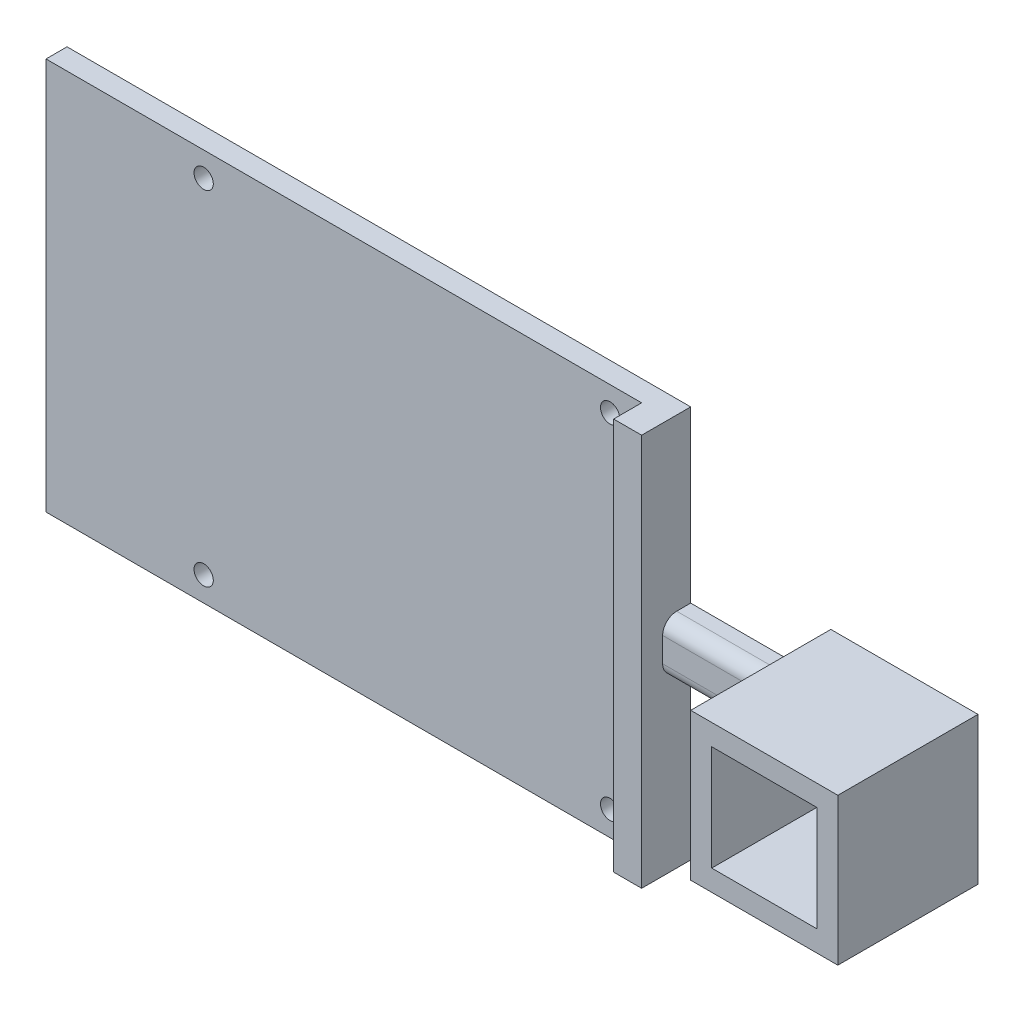
SolidWorks part; units mm, degrees
ref_plane "Front Plane" through (0, 0, 0) normal (0, 0, 1) x (1, 0, 0)
ref_plane "Top Plane" through (0, 0, 0) normal (0, 1, 0) x (1, 0, 0)
ref_plane "Right Plane" through (0, 0, 0) normal (1, 0, 0) x (0, 0, -1)
sketch "Sketch2" plane through (0, 0, 0) normal (0, 0, 1) x (1, 0, 0)
  line L1 (10.5, -10.5) -> (-10.5, -10.5)
  line L2 (10.5, -10.5) -> (10.5, 10.5)
  line L3 (10.5, 10.5) -> (-10.5, 10.5)
  line L4 (-10.5, -10.5) -> (-10.5, 10.5)
  line L5 (10.5, -10.5) -> (-10.5, 10.5) construction
  line L6 (10.5, 10.5) -> (-10.5, -10.5) construction
  point P0 (0, 0)
  dimension "D1" = 21
extrude "Boss-Extrude1" add sketch "Sketch2" along normal blind 20
sketch "Sketch3" plane through (0, 0, 20) normal (0, 0, 1) x (1, 0, 0)
  line L1 (7.5, -7.5) -> (-7.5, -7.5)
  line L2 (7.5, -7.5) -> (7.5, 7.5)
  line L3 (7.5, 7.5) -> (-7.5, 7.5)
  line L4 (-7.5, -7.5) -> (-7.5, 7.5)
  line L5 (7.5, -7.5) -> (-7.5, 7.5) construction
  line L6 (7.5, 7.5) -> (-7.5, -7.5) construction
  point P0 (0, 0)
  dimension "D1" = 15
  dimension "D2" = 15
extrude "Cut-Extrude1" cut sketch "Sketch3" against normal blind 20
sketch "Sketch4" plane through (-10.5, 0, 0) normal (-1, 0, 0) x (0, 0, 1)
  line L1 (0, 3.75) -> (4, 3.75)
  line L2 (0, 3.75) -> (0, -3.75)
  line L3 (0, -3.75) -> (4, -3.75)
  line L4 (4, 3.75) -> (4, -3.75)
  point P4 (0, 0)
  dimension "D1" = 7.5
  dimension "D2" = 4
  dimension "D3" = 10.5
extrude "Boss-Extrude2" add sketch "Sketch4" along normal blind 20
fillet "Fillet2" radius 2 2 edges at (-20.5, -3.75, 4) (-20.5, 3.75, 4)
sketch "Sketch5" plane through (-30.5, 0, 0) normal (-1, 0, 0) x (0, 0, 1)
  line L0 (0, 0) -> (4, 0) construction
  line L1 (0, -28) -> (7, -28)
  line L2 (0, -28) -> (0, 28)
  line L3 (0, 28) -> (7, 28)
  line L4 (7, -28) -> (7, 28)
  line L5 (4, -1.75) -> (4, 1.75) construction
  line L6 (0, 0) -> (7, 0) construction
  dimension "D1" = 56
  dimension "D2" = 7
extrude "Boss-Extrude3" add sketch "Sketch5" along normal blind 4
sketch "Sketch6" plane through (-34.5, 0, 0) normal (-1, 0, 0) x (0, 0, 1)
  line L0 (0, -28) -> (7, -28) construction
  line L1 (0, 28) -> (3, 28)
  line L2 (0, 28) -> (0, -28)
  line L3 (0, -28) -> (3, -28)
  line L4 (3, 28) -> (3, -28)
  dimension "D1" = 3
extrude "Boss-Extrude4" add sketch "Sketch6" along normal blind 85
sketch "Sketch8" plane through (0, 0, 3) normal (0, 0, 1) x (1, 0, 0)
  line L0 (-34.5, -28) -> (-34.5, 28) construction
  line L1 (-119.5, -28) -> (-34.5, -28) construction
  circle A0 centre (-39, -24.5) radius 1.375
  circle A1 centre (-39, 24.5) radius 1.375
  circle A2 centre (-97, -24.5) radius 1.375
  circle A3 centre (-97, 24.5) radius 1.375
  point P12 (0, 0)
  point P13 (0, 0)
  point P14 (0, 0)
  dimension "D1" = 2.75
  dimension "D2" = 2.75
  dimension "D3" = 2.75
  dimension "D4" = 2.75
  dimension "D5" = 58
  dimension "D6" = 49
  dimension "D7" = 4.5
  dimension "D8" = 3.5
extrude "Cut-Extrude2" cut sketch "Sketch8" against normal blind 4
